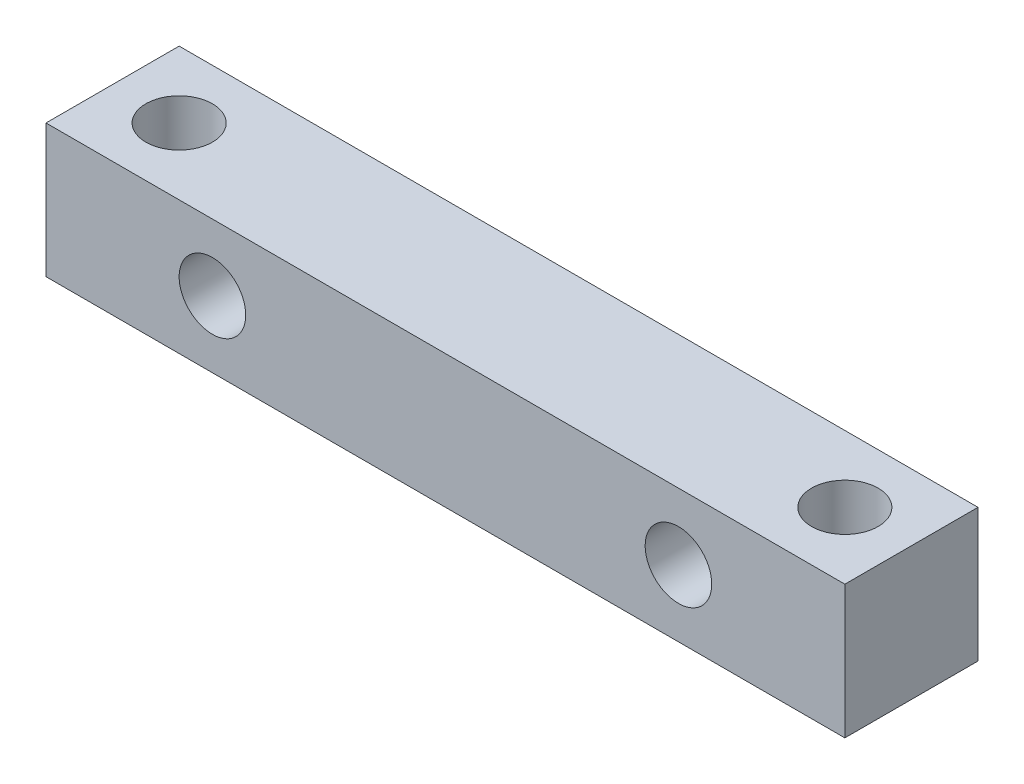
SolidWorks part; units mm, degrees
ref_plane "Plan de face" through (0, 0, 0) normal (0, 0, 1) x (1, 0, 0)
ref_plane "Plan de dessus" through (0, 0, 0) normal (0, 1, 0) x (1, 0, 0)
ref_plane "Plan de droite" through (0, 0, 0) normal (1, 0, 0) x (0, 0, -1)
sketch "Esquisse1" plane through (0, 0, 0) normal (0, 1, 0) x (1, 0, 0)
  line L1 (-18, 3) -> (18, 3)
  line L2 (-18, 3) -> (-18, -3)
  line L3 (-18, -3) -> (18, -3)
  line L4 (18, 3) -> (18, -3)
  dimension "D1" = 6
  dimension "D2" = 36
  dimension "D3" = 3
  dimension "D4" = 18
extrude "Boss.-Extru.1" add sketch "Esquisse1" along normal blind 6
sketch "Esquisse2" plane through (0, 6, 0) normal (0, 1, 0) x (1, 0, 0)
  line L0 (-18, 3) -> (-18, -3) construction
  line L1 (18, 3) -> (-18, 3) construction
  circle A0 centre (-15, 0) radius 1.5
  point P2 (-18, 0)
  dimension "D1" = 3
  dimension "D2" = 3
  dimension "D3" = 3
extrude "Enlèv. mat.-Extru.1" cut sketch "Esquisse2" against normal blind 60
mirror "Symétrie1" about plane through (0, 0, 0) normal (1, 0, 0) of "Enlèv. mat.-Extru.1"
sketch "Esquisse3" plane through (0, 0, 3) normal (0, 0, 1) x (1, 0, 0)
  line L0 (-18, 6) -> (18, 6) construction
  line L1 (-18, 6) -> (-18, 0) construction
  circle A0 centre (-10.5, 3) radius 1.5
  dimension "D1" = 3
  dimension "D2" = 3
  dimension "D3" = 7.5
extrude "Enlèv. mat.-Extru.2" cut sketch "Esquisse3" against normal blind 6
mirror "Symétrie2" about plane through (0, 0, 0) normal (1, 0, 0) of "Enlèv. mat.-Extru.2"
